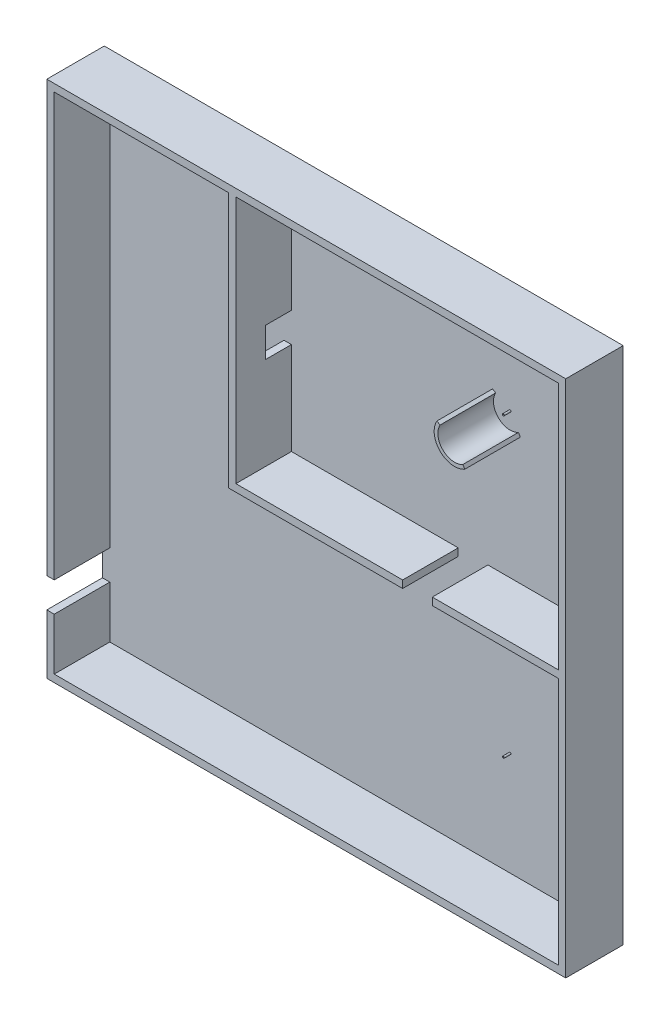
SolidWorks part; units mm, degrees
ref_plane "前视基准面" through (0, 0, 0) normal (0, 0, 1) x (1, 0, 0)
ref_plane "上视基准面" through (0, 0, 0) normal (0, 1, 0) x (1, 0, 0)
ref_plane "右视基准面" through (0, 0, 0) normal (1, 0, 0) x (0, 0, -1)
other "Configuration Table"
sketch "草图1" plane through (0, 0, 0) normal (0, 0, 1) x (1, 0, 0)
  line L1 (-7000, 7000) -> (7000, 7000)
  line L2 (-7000, 7000) -> (-7000, -7000)
  line L3 (-7000, -7000) -> (7000, -7000)
  line L4 (7000, 7000) -> (7000, -7000)
  line L5 (-7000, 7000) -> (7000, -7000) construction
  line L6 (-7000, -7000) -> (7000, 7000) construction
  point P0 (0, 0)
  dimension "D1" = 14000
  dimension "D2" = 14000
extrude "凸台-拉伸1" add sketch "草图1" against normal blind 50
sketch "草图2" plane through (0, 0, 0) normal (0, 0, 1) x (1, 0, 0)
  line L0 (-7000, 7000) -> (7000, 7000)
  line L5 (7000, 7000) -> (7000, -7000)
  line L6 (7000, -7000) -> (-7000, -7000)
  line L11 (-7000, -7000) -> (-7000, -5400)
  line L12 (-7000, 7000) -> (-7000, -7000) construction
  line L13 (-7000, -5400) -> (-6800, -5400)
  line L14 (-6800, -5400) -> (-6800, -6800)
  line L15 (-6800, -6800) -> (6800, -6800)
  line L16 (6800, -6800) -> (6800, -100)
  line L17 (6800, 6800) -> (-1900, 6800)
  line L18 (-6800, 6800) -> (-6800, -4600)
  line L19 (-6800, -4600) -> (-7000, -4600)
  line L20 (-7000, -4600) -> (-7000, 7000)
  line L21 (7000, -7000) -> (7000, 7000) construction
  line L22 (-7000, -7000) -> (7000, -7000) construction
  line L23 (6800, -100) -> (3400, -100)
  line L24 (3400, -100) -> (3400, 100)
  line L25 (3400, 100) -> (6800, 100)
  line L26 (2600, 100) -> (2600, -100)
  line L27 (2600, -100) -> (-2100, -100)
  line L28 (-2100, -100) -> (-2100, 2600)
  line L29 (-2100, 2600) -> (-1900, 2600)
  line L30 (-1900, 2600) -> (-1900, 100)
  line L31 (-1900, 100) -> (2600, 100)
  line L32 (-1900, 6800) -> (-1900, 3400)
  line L33 (-1900, 3400) -> (-2100, 3400)
  line L34 (-2100, 3400) -> (-2100, 6800)
  line L35 (3523.686, 4275) -> (3610.2886, 4225)
  line L36 (4275, 3523.686) -> (4225, 3610.2886)
  line L37 (-2100, 6800) -> (-6800, 6800)
  line L38 (6800, 100) -> (6800, 6800)
  circle A0 centre (4000, -4000) radius 10
  circle A1 centre (4000, -4000) radius 25
  circle A2 centre (4000, 4000) radius 10
  circle A3 centre (4000, 4000) radius 25
  arc A4 (3610.2886, 4225) -> (4225, 3610.2886) centre (4000, 4000) ccw
  arc A5 (3523.686, 4275) -> (4275, 3523.686) centre (4000, 4000) ccw
  point P0 (0, 0)
  point P7 (0, 0)
  dimension "D19" = 900
  dimension "D20" = 1100
  dimension "D21" = 20
  dimension "D22" = 50
  dimension "D25" = 20
  dimension "D26" = 50
  dimension "D1" = 200
  dimension "D2" = 200
  dimension "D3" = 200
  dimension "D4" = 200
  dimension "D5" = 1600
  dimension "D6" = 2400
  dimension "D7" = 100
  dimension "D8" = 100
  dimension "D9" = 3600
  dimension "D10" = 4400
  dimension "D11" = 3600
  dimension "D12" = 4400
  dimension "D13" = 8900
  dimension "D14" = 9100
  dimension "D15" = 3000
  dimension "D16" = 3000
  dimension "D17" = 3000
  dimension "D18" = 3000
  dimension "D23" = 30
  dimension "D24" = 60
extrude "凸台-拉伸2" add sketch "草图2" along normal blind 1500
sketch "草图3" plane through (0, 0, 1500) normal (0, 0, 1) x (1, 0, 0)
  circle A1 centre (4000, 4000) radius 25
  circle A2 centre (4000, 4000) radius 25
  circle A3 centre (4000, -4000) radius 25
  circle A4 centre (4000, -4000) radius 25
  dimension "D1" = 0
  dimension "D2" = 0
extrude "切除-拉伸1" cut sketch "草图3" against normal blind 1300
ref_axis "基准轴1" through (4000, -4000, 800) along (0, 0, -1)
ref_plane "基准面1" through (0, -4000, 0) normal (0, 1, 0) x (1, 0, 0)
sketch "草图5" plane through (0, -4000, 0) normal (0, 1, 0) x (1, 0, 0)
  line L0 (4000, -800) -> (4000, 0) construction
  line L1 (-7000, 50) -> (7000, 50) construction
  line L2 (4000, -230) -> (4000, -170)
  arc A0 (4000, -170) -> (4000, -230) centre (4000, -200) ccw
  dimension "D1" = 60
  dimension "D2" = 0
  dimension "D3" = 250
revolve "切除-旋转2" cut sketch "草图5" angle 360 about axis through (4000, -4000, 800) along (0, 0, -1)
mirror "镜向1" about plane through (0, 0, 0) normal (0, 1, 0) of "切除-旋转2"
sketch "草图6" plane through (0, 0, 1500) normal (0, 0, 1) x (1, 0, 0)
  line L0 (-2100, 3671.9437) -> (-1900, 3671.9437)
  line L1 (-2100, 6800) -> (-2100, 3400) construction
  line L2 (-1900, 3400) -> (-1900, 6800) construction
  line L3 (-1900, 3671.9437) -> (-1900, 2152.2899)
  line L4 (-1900, 100) -> (-1900, 2600) construction
  line L5 (-1900, 2152.2899) -> (-2100, 2152.2899)
  line L6 (-2100, 2600) -> (-2100, -100) construction
  line L7 (-2100, 2152.2899) -> (-2100, 3671.9437)
extrude "凸台-拉伸3" add sketch "草图6" against normal blind 800
